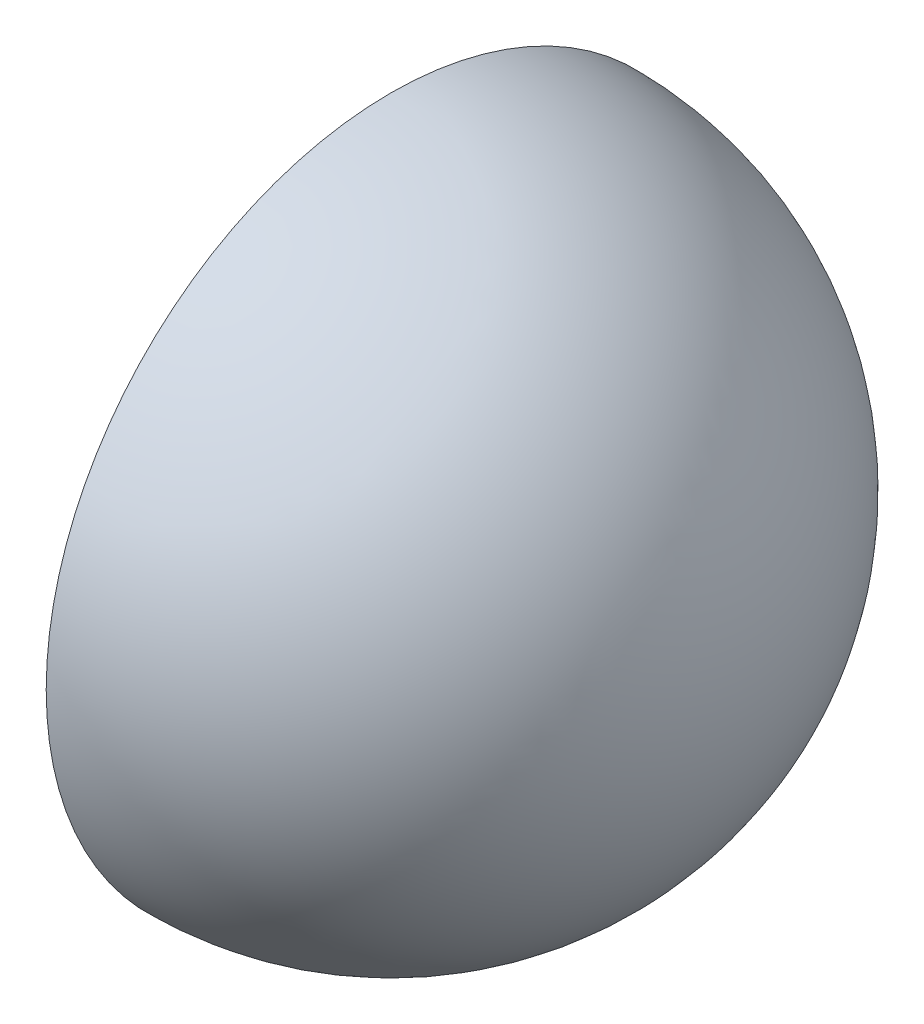
SolidWorks part; units mm, degrees
ref_plane "Front Plane" through (0, 0, 0) normal (0, 0, 1) x (1, 0, 0)
ref_plane "Top Plane" through (0, 0, 0) normal (0, 1, 0) x (1, 0, 0)
ref_plane "Right Plane" through (0, 0, 0) normal (1, 0, 0) x (0, 0, -1)
sketch "Sketch28" plane through (0, 0, 0) normal (0, 0, 1) x (1, 0, 0)
  line L0 (0, 0) -> (37.5, 0)
  line L1 (0, -37.5) -> (0, 0)
  arc A0 (37.5, 0) -> (0, -37.5) centre (0, 0) cw
revolve "Revolve1" add sketch "Sketch28" angle 360 about L0
shell "Shell1" thickness 1
